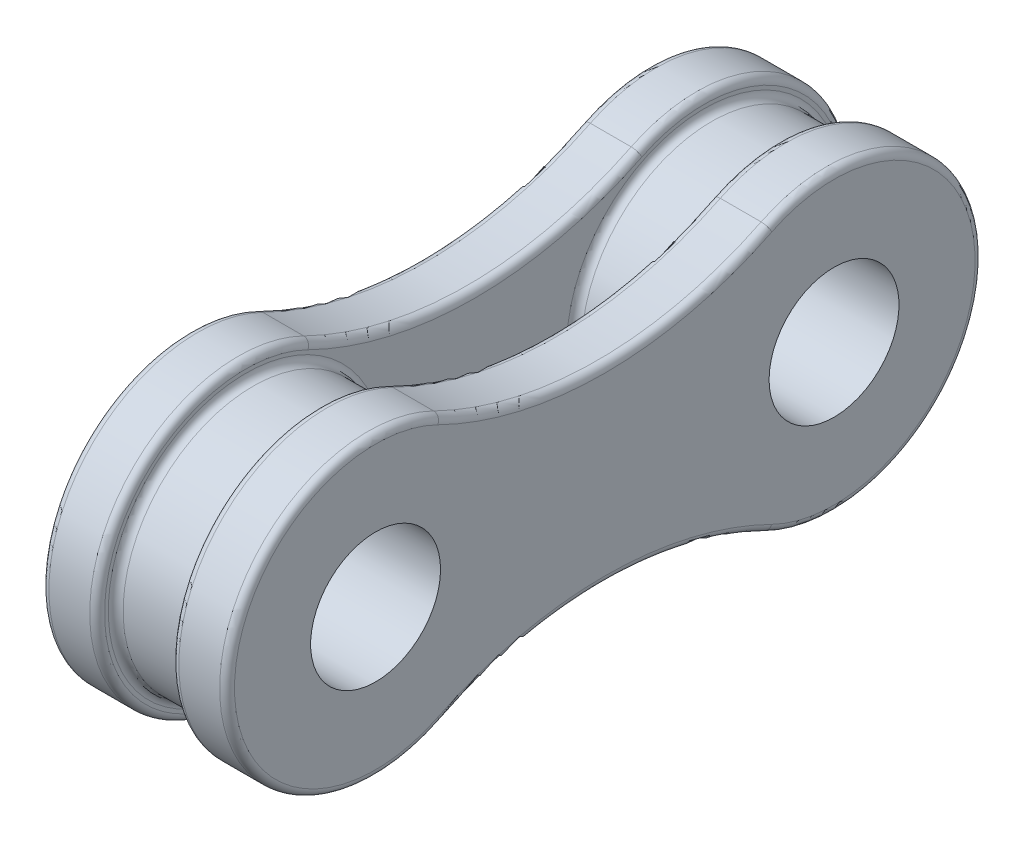
SolidWorks part; units mm, degrees
ref_plane "Alzado" through (0, 0, 0) normal (0, 0, 1) x (1, 0, 0)
ref_plane "Planta" through (0, 0, 0) normal (0, 1, 0) x (1, 0, 0)
ref_plane "Vista lateral" through (0, 0, 0) normal (1, 0, 0) x (0, 0, -1)
sketch "Croquis1" plane through (0, 0, 0) normal (1, 0, 0) x (0, 0, -1)
  line L0 (-6.175, 0) -> (6.175, 0) construction
  line L1 (0, 3.438) -> (0, -3.438) construction
  circle A0 centre (-6.175, 0) radius 1.75
  arc A1 (-4.4107, 3.5899) -> (-4.4107, -3.5899) centre (-6.175, 0) ccw
  circle A2 centre (6.175, 0) radius 1.75
  arc A3 (4.4107, 3.5899) -> (4.4107, -3.5899) centre (6.175, 0) cw
  arc A4 (-4.4107, 3.5899) -> (4.4107, 3.5899) centre (0, 12.5646) ccw
  arc A5 (-4.4107, -3.5899) -> (4.4107, -3.5899) centre (0, -12.5646) cw
  point P4 (0, 0)
  point P8 (0, 0)
  dimension "D2" = 8
  dimension "D3" = 3.5
  dimension "D4" = 10
  dimension "D1" = 12.35
extrude "Saliente-Extruir1" add sketch "Croquis1" along normal blind 1.5 from offset 1
sketch "Croquis2" plane through (0, 0, 0) normal (1, 0, 0) x (0, 0, -1)
  circle A0 centre (6.175, 0) radius 1.75 construction
  circle A1 centre (-6.175, 0) radius 1.75 construction
  circle A2 centre (6.175, 0) radius 1.75
  circle A3 centre (-6.175, 0) radius 1.75
  arc A4 (-4.4107, 3.5899) -> (4.4107, 3.5899) centre (0, 12.5646) ccw
  arc A5 (-4.4107, 3.5899) -> (-4.4107, -3.5899) centre (-6.175, 0) ccw
  arc A6 (4.4107, -3.5899) -> (-4.4107, -3.5899) centre (0, -12.5646) ccw
  arc A7 (4.4107, -3.5899) -> (4.4107, 3.5899) centre (6.175, 0) ccw
  arc A8 (-4.4107, 3.5899) -> (4.4107, 3.5899) centre (0, 12.5646) ccw
  arc A9 (-4.4107, 3.5899) -> (-4.4107, -3.5899) centre (-6.175, 0) ccw
  arc A10 (4.4107, -3.5899) -> (-4.4107, -3.5899) centre (0, -12.5646) ccw
  arc A11 (4.4107, -3.5899) -> (4.4107, 3.5899) centre (6.175, 0) ccw
  dimension "D1" = 0
extrude "Saliente-Extruir2" add sketch "Croquis2" against normal blind 1.5 from offset 1 separate body offset against normal yes
sketch "Croquis3" plane through (0, 0, 0) normal (1, 0, 0) x (0, 0, -1)
  circle A0 centre (6.175, 0) radius 1.75 construction
  circle A1 centre (-6.175, 0) radius 1.75 construction
  circle A2 centre (6.175, 0) radius 1.75
  circle A3 centre (-6.175, 0) radius 1.75
  circle A4 centre (-6.175, 0) radius 3.5
  circle A5 centre (6.175, 0) radius 3.5
  dimension "D1" = 7
extrude "Saliente-Extruir3" add sketch "Croquis3" along normal up to next (1 mm away) and the other way up to next (2.5 mm away)
fillet "Redondeo1" radius 0.2 22 edges at (2.5, 0, -10.175) (2.5, -2.5646, 0) (2.5, 0, 10.175) (1, 0, 10.175) (1, -2.5646, 0) (1, 0, -10.175) (1, 2.5646, 0) (1, 0, -9.675) (1, 0, 2.675) (-1, 2.5646, 0) (-1, 0, -10.175) (-1, -2.5646, 0) (-1, 0, 10.175) (-1, 0, -9.675) (-1, 0, 2.675) (-2.5, -2.5646, 0) (-2.5, 0, -10.175) (-2.5, 2.5646, 0) (-2.5, 0, 10.175) (-2.5, 0, -7.925) (-2.5, 0, 4.425) (2.5, 2.5646, 0)
